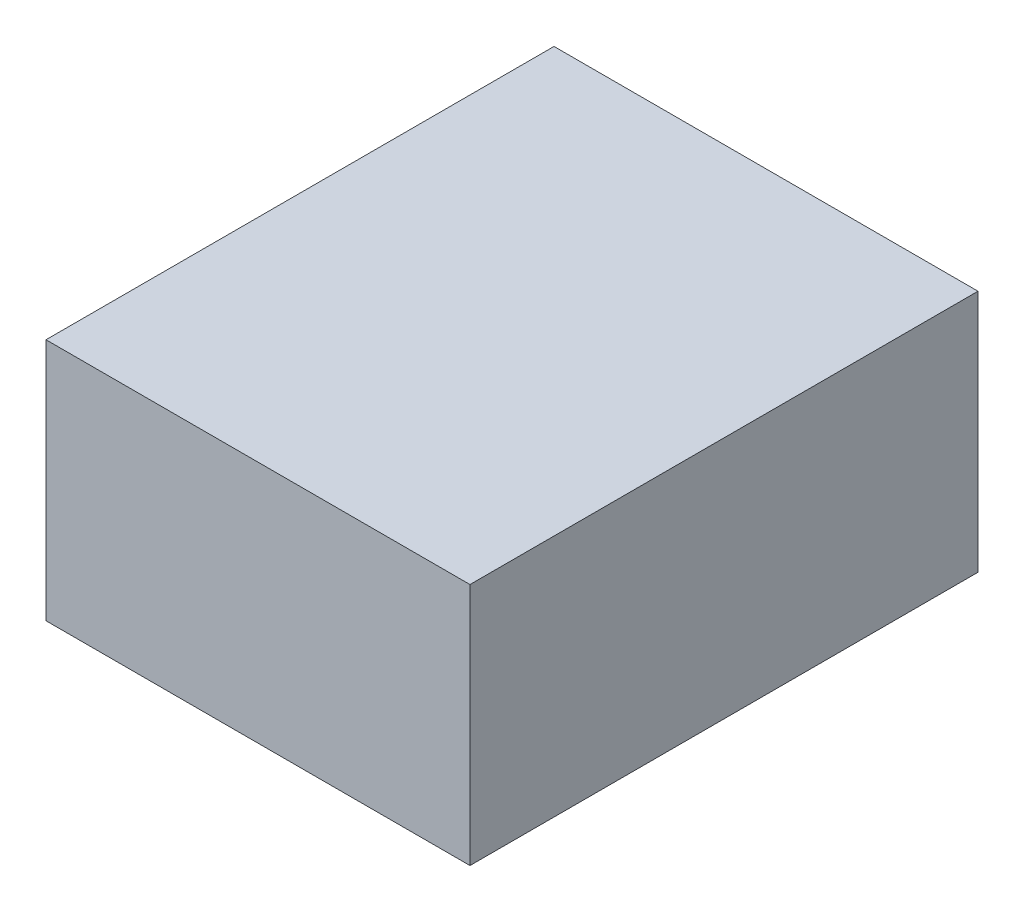
SolidWorks part; units mm, degrees
ref_plane "Front Plane" through (0, 0, 0) normal (0, 0, 1) x (1, 0, 0)
ref_plane "Top Plane" through (0, 0, 0) normal (0, 1, 0) x (1, 0, 0)
ref_plane "Right Plane" through (0, 0, 0) normal (1, 0, 0) x (0, 0, -1)
sketch "Sketch1" plane through (0, 0, 0) normal (0, 1, 0) x (1, 0, 0)
  line L1 (43.5492, -52.1822) -> (-43.5492, -52.1822)
  line L2 (43.5492, -52.1822) -> (43.5492, 52.1822)
  line L3 (43.5492, 52.1822) -> (-43.5492, 52.1822)
  line L4 (-43.5492, -52.1822) -> (-43.5492, 52.1822)
  line L5 (43.5492, -52.1822) -> (-43.5492, 52.1822) construction
  line L6 (43.5492, 52.1822) -> (-43.5492, -52.1822) construction
  point P0 (0, 0)
extrude "Boss-Extrude1" add sketch "Sketch1" along normal blind 50
